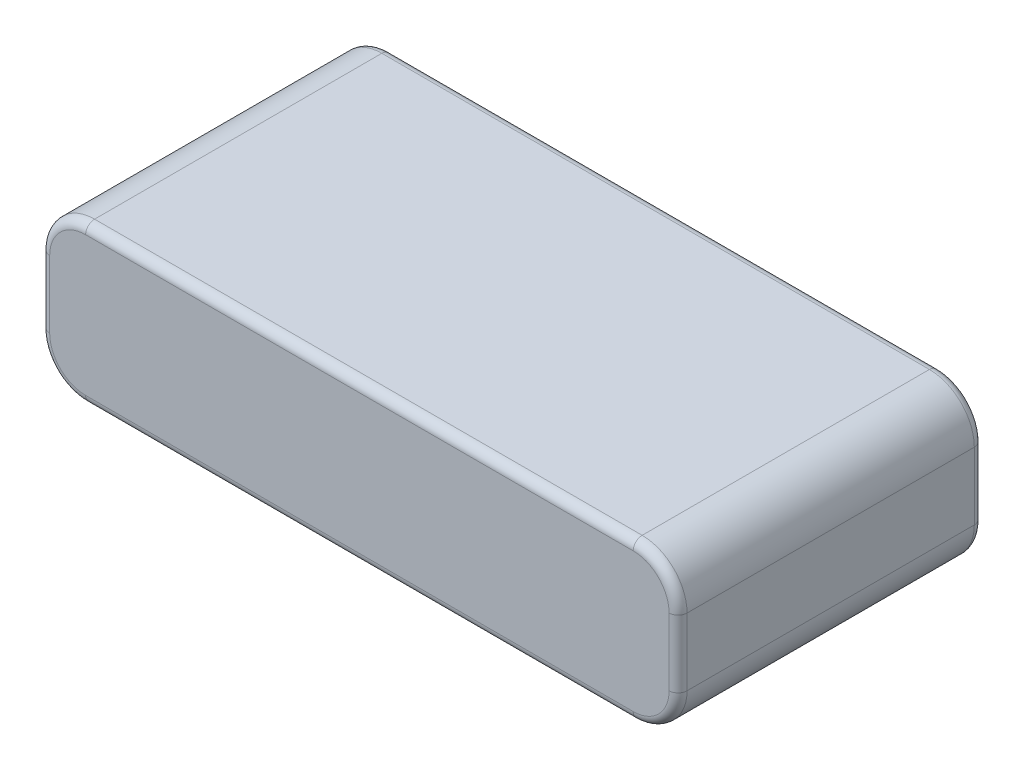
SolidWorks part; units mm, degrees
ref_plane "Front Plane" through (0, 0, 0) normal (0, 0, 1) x (1, 0, 0)
ref_plane "Top Plane" through (0, 0, 0) normal (0, 1, 0) x (1, 0, 0)
ref_plane "Right Plane" through (0, 0, 0) normal (1, 0, 0) x (0, 0, -1)
sketch "Sketch1" plane through (0, 0, 0) normal (0, 1, 0) x (1, 0, 0)
  line L1 (-35.5, 17) -> (35.5, 17)
  line L2 (-35.5, 17) -> (-35.5, -17)
  line L3 (-35.5, -17) -> (35.5, -17)
  line L4 (35.5, 17) -> (35.5, -17)
  line L5 (-35.5, 17) -> (35.5, -17) construction
  line L6 (-35.5, -17) -> (35.5, 17) construction
  point P0 (0, 0)
  dimension "D1" = 71
  dimension "D2" = 34
extrude "Boss-Extrude1" add sketch "Sketch1" along normal blind 17.5
fillet "Fillet1" radius 5 4 edges at (-35.5, 0, 0) (35.5, 0, 0) (35.5, 17.5, 0) (-35.5, 17.5, 0)
fillet "Fillet2" radius 1 16 edges at (34.0355, 1.4645, -17) (35.5, 8.75, -17) (34.0355, 16.0355, -17) (0, 17.5, -17) (-34.0355, 16.0355, -17) (-35.5, 8.75, -17) (-34.0355, 1.4645, -17) (0, 0, -17) (-34.0355, 16.0355, 17) (0, 17.5, 17) (34.0355, 16.0355, 17) (35.5, 8.75, 17) (34.0355, 1.4645, 17) (0, 0, 17) (-34.0355, 1.4645, 17) (-35.5, 8.75, 17)
